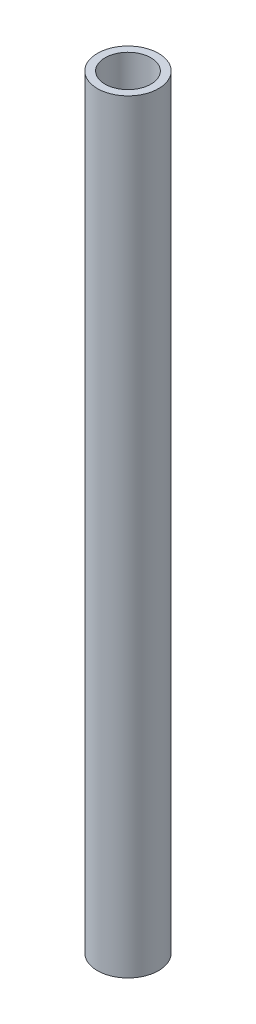
SolidWorks part; units mm, degrees
material "Thornel VCB-20 탄소 섬유"
ref_plane "정면" through (0, 0, 0) normal (0, 0, 1) x (1, 0, 0)
ref_plane "윗면" through (0, 0, 0) normal (0, 1, 0) x (1, 0, 0)
ref_plane "우측면" through (0, 0, 0) normal (1, 0, 0) x (0, 0, -1)
sketch "스케치1" plane through (0, 0, 0) normal (0, 1, 0) x (1, 0, 0)
  circle A0 centre (0, 0) radius 10
  circle A1 centre (0, 0) radius 7.5
  dimension "D1" = 20
  dimension "D2" = 15
extrude "보스-돌출1" add sketch "스케치1" along normal blind 250
